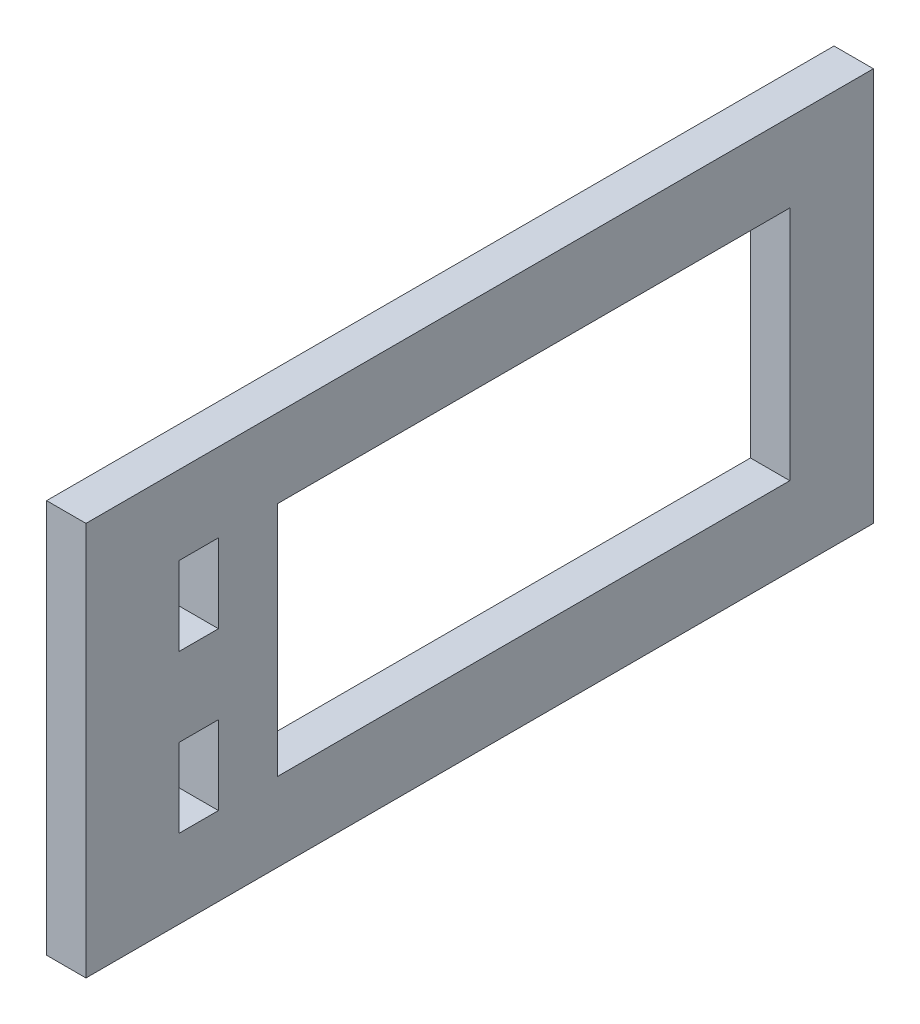
SolidWorks part; units mm, degrees
ref_plane "Front Plane" through (0, 0, 0) normal (0, 0, 1) x (1, 0, 0)
ref_plane "Top Plane" through (0, 0, 0) normal (0, 1, 0) x (1, 0, 0)
ref_plane "Right Plane" through (0, 0, 0) normal (1, 0, 0) x (0, 0, -1)
sketch "Sketch1" plane through (0, 0, 0) normal (1, 0, 0) x (0, 0, -1)
  line L1 (0, 0) -> (-100, 0)
  line L2 (0, 0) -> (0, 50)
  line L3 (0, 50) -> (-100, 50)
  line L4 (-100, 0) -> (-100, 50)
  line L5 (-88.174, 40) -> (-83.174, 40)
  line L6 (-88.174, 40) -> (-88.174, 30)
  line L7 (-88.174, 30) -> (-83.174, 30)
  line L8 (-83.174, 40) -> (-83.174, 30)
  line L9 (-88.174, 20) -> (-83.174, 20)
  line L10 (-88.174, 20) -> (-88.174, 10)
  line L11 (-88.174, 10) -> (-83.174, 10)
  line L12 (-83.174, 20) -> (-83.174, 10)
  line L13 (-75.6517, 40) -> (-10.6154, 40)
  line L14 (-75.6517, 40) -> (-75.6517, 10)
  line L15 (-75.6517, 10) -> (-10.6154, 10)
  line L16 (-10.6154, 40) -> (-10.6154, 10)
  dimension "D1" = 100
  dimension "D2" = 50
  dimension "D3" = 10
  dimension "D4" = 5
  dimension "D5" = 10
  dimension "D6" = 10
  dimension "D7" = 5
  dimension "D8" = 10
extrude "Boss-Extrude3" add sketch "Sketch1" along normal blind 5
